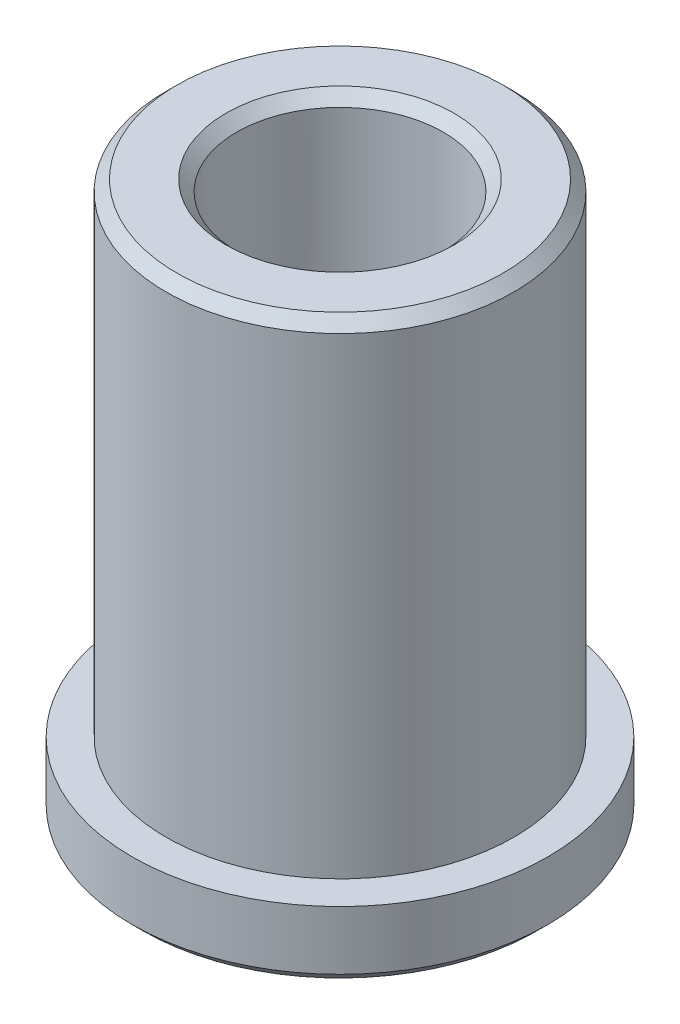
SolidWorks part; units mm, degrees
material "Tin Bearing Bronze"
ref_plane "Front Plane" through (0, 0, 0) normal (0, 0, 1) x (1, 0, 0)
ref_plane "Top Plane" through (0, 0, 0) normal (0, 1, 0) x (1, 0, 0)
ref_plane "Right Plane" through (0, 0, 0) normal (1, 0, 0) x (0, 0, -1)
sketch "Sketch1" plane through (0, 0, 0) normal (0, 0, 1) x (1, 0, 0)
  line L0 (-2.375, 0) -> (-2.375, 12.7125)
  line L1 (-2.375, 12.7125) -> (-4, 12.7125)
  line L2 (-4, 12.7125) -> (-4, 1.6)
  line L3 (-4, 1.6) -> (-4.78, 1.6)
  line L4 (-4.78, 1.6) -> (-4.78, 0)
  line L5 (-4.78, 0) -> (-2.375, 0)
  line L6 (0, 0) -> (0, 30.0257) construction
  dimension "D1" = 4.75
  dimension "D2" = 9.56
  dimension "D3" = 1.6
  dimension "D4" = 11.1125
  dimension "D5" = 8
revolve "Revolve1" add sketch "Sketch1" angle 360 about L6
chamfer "Chamfer1" distance 0.25 angle 45 4 edges at (0, 0, -4.78) (0, 0, -2.375) (0, 12.7125, -2.375) (0, 12.7125, -4)
